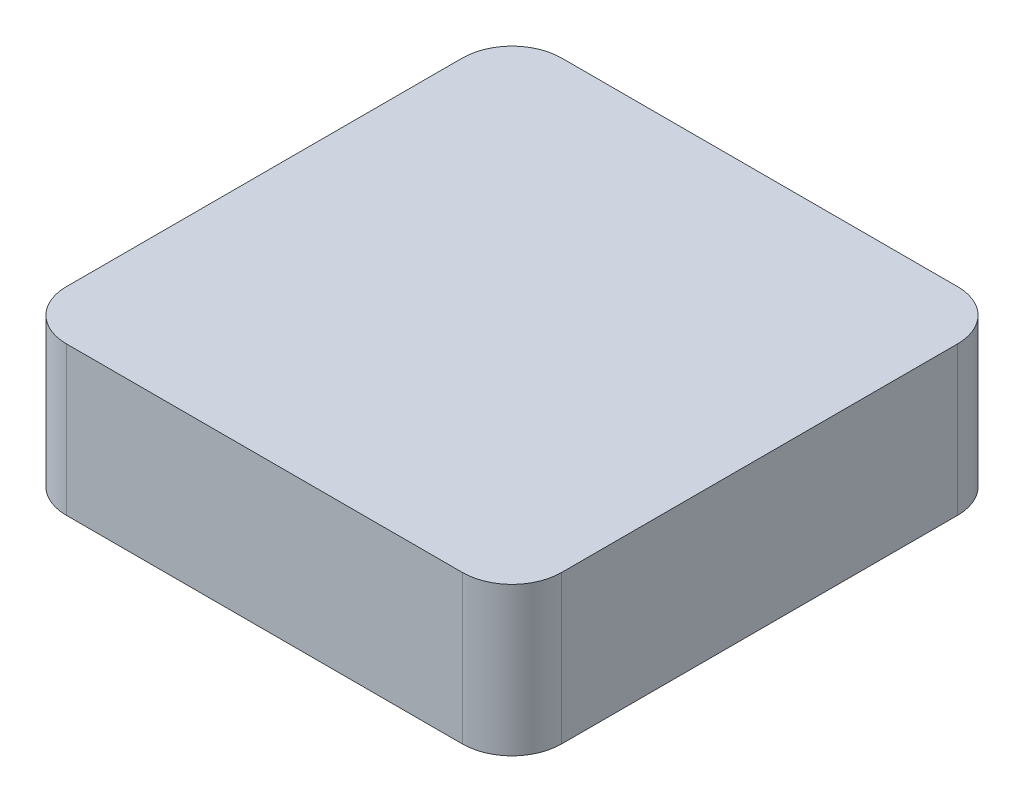
SolidWorks part; units mm, degrees
material "Pine"
ref_plane "Front Plane" through (0, 0, 0) normal (0, 0, 1) x (1, 0, 0)
ref_plane "Top Plane" through (0, 0, 0) normal (0, 1, 0) x (1, 0, 0)
ref_plane "Right Plane" through (0, 0, 0) normal (1, 0, 0) x (0, 0, -1)
sketch "Sketch1" plane through (0, 0, 0) normal (0, 1, 0) x (1, 0, 0)
  line L1 (-50.8, -63.5) -> (50.8, -63.5)
  line L2 (-63.5, -50.8) -> (-63.5, 50.8)
  line L3 (-50.8, 63.5) -> (50.8, 63.5)
  line L4 (63.5, -50.8) -> (63.5, 50.8)
  line L5 (-63.5, -63.5) -> (63.5, 63.5) construction
  line L6 (-63.5, 63.5) -> (63.5, -63.5) construction
  arc A0 (50.8, 63.5) -> (63.5, 50.8) centre (50.8, 50.8) cw
  arc A1 (50.8, -63.5) -> (63.5, -50.8) centre (50.8, -50.8) ccw
  arc A2 (-50.8, -63.5) -> (-63.5, -50.8) centre (-50.8, -50.8) cw
  arc A3 (-63.5, 50.8) -> (-50.8, 63.5) centre (-50.8, 50.8) cw
  point P0 (0, 0)
  dimension "D3" = 12.7
  dimension "D1" = 127
extrude "Boss-Extrude1" add sketch "Sketch1" along normal blind 38.1
